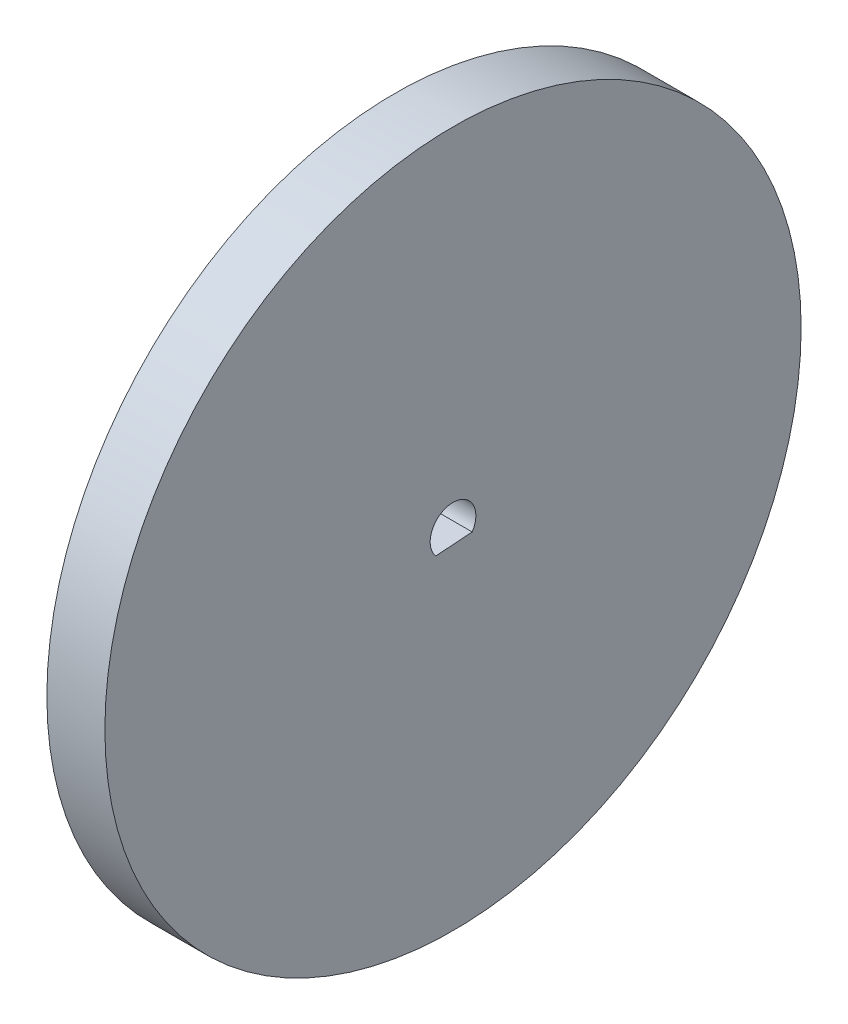
SolidWorks part; units mm, degrees
ref_plane "Front Plane" through (0, 0, 0) normal (0, 0, 1) x (1, 0, 0)
ref_plane "Top Plane" through (0, 0, 0) normal (0, 1, 0) x (1, 0, 0)
ref_plane "Right Plane" through (0, 0, 0) normal (1, 0, 0) x (0, 0, -1)
sketch "Sketch1" plane through (0, 0, 0) normal (1, 0, 0) x (0, 0, -1)
  circle A0 centre (0, 0) radius 38.1
  dimension "D1" = 76.2
extrude "Boss-Extrude1" add sketch "Sketch1" along normal blind 6.35
sketch "Sketch5" plane through (6.35, 0, 0) normal (1, 0, 0) x (0, 0, -1)
  line L0 (-1.8893, -1.6372) -> (2.1007, -1.3553) construction
  line L1 (-1.8893, -1.6372) -> (2.1007, -1.3553)
  arc A0 (2.1007, -1.3553) -> (-1.8893, -1.6372) centre (0, 0) ccw construction
  arc A3 (2.1007, -1.3553) -> (-1.8893, -1.6372) centre (0, 0) ccw
extrude "Cut-Extrude1" cut sketch "Sketch5" against normal through all
equation "\"material\"=\"GMaterial@Platform.assembly\""
equation "\"D1@Boss-Extrude1\"=\"material\""
